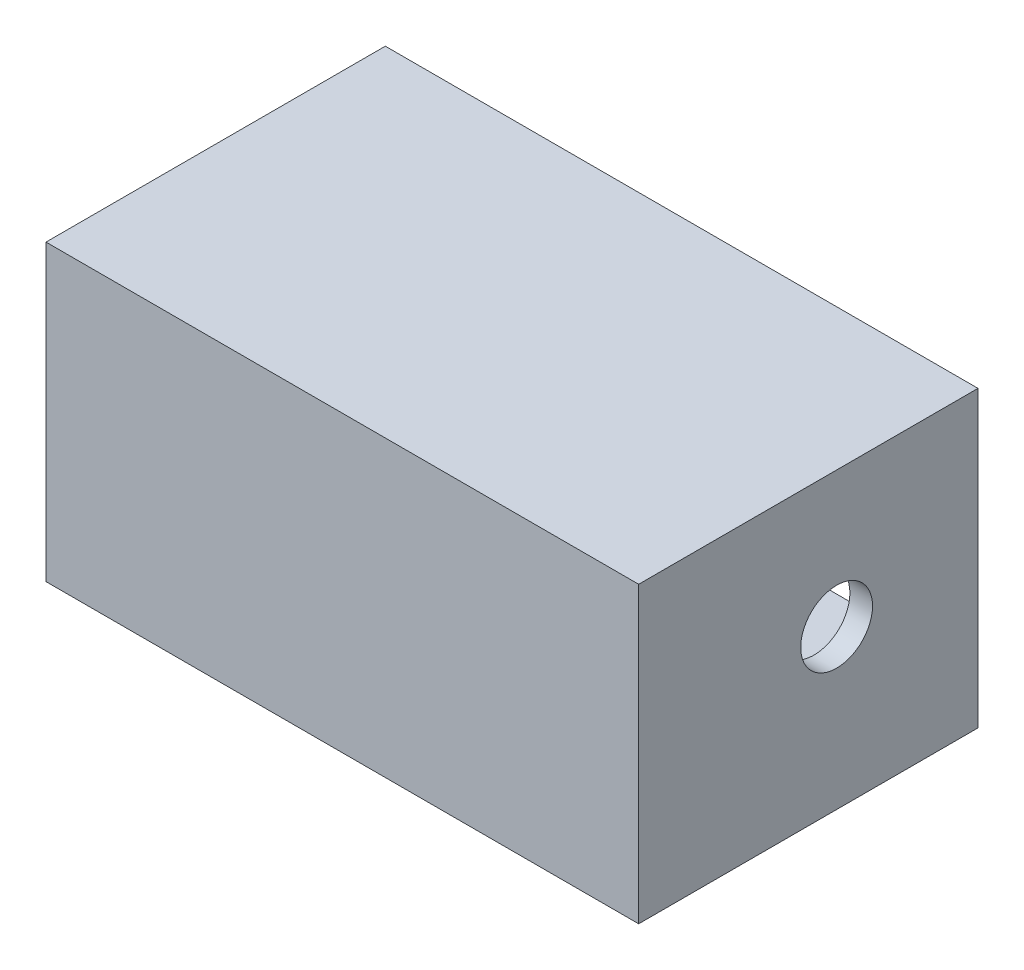
SolidWorks part; units mm, degrees
ref_plane "Front Plane" through (0, 0, 0) normal (0, 0, 1) x (1, 0, 0)
ref_plane "Top Plane" through (0, 0, 0) normal (0, 1, 0) x (1, 0, 0)
ref_plane "Right Plane" through (0, 0, 0) normal (1, 0, 0) x (0, 0, -1)
sketch "Sketch1" plane through (0, 0, 0) normal (0, 1, 0) x (1, 0, 0)
  line L1 (0, 0) -> (262, 0)
  line L2 (0, 0) -> (0, 150)
  line L3 (0, 150) -> (262, 150)
  line L4 (262, 0) -> (262, 150)
extrude "Boss-Extrude1" add sketch "Sketch1" along normal blind 20
sketch "Sketch2" plane through (0, 20, 0) normal (0, 1, 0) x (1, 0, 0)
  line L1 (0, 0) -> (262, 0)
  line L3 (10, 10) -> (252, 10)
  line L5 (262, 150) -> (0, 150) construction
  line L7 (0, 0) -> (0, 150)
  line L8 (0, 150) -> (10, 150)
  line L9 (10, 10) -> (10, 150)
  line L11 (262, 150) -> (252, 150)
  line L12 (262, 150) -> (262, 0)
  line L14 (252, 150) -> (252, 10)
  point P1 (0, 0)
extrude "Boss-Extrude2" add sketch "Sketch2" along normal blind 100
sketch "Sketch3" plane through (10, 0, 0) normal (1, 0, 0) x (0, 0, -1)
  circle A0 centre (87.5, 70) radius 14.2875
sketch "Sketch4" plane through (252, 0, 0) normal (1, 0, 0) x (0, 0, -1)
  circle A0 centre (87.5, 70) radius 15.875
extrude "Cut-Extrude1" cut sketch "Sketch3" against normal through all
extrude "Cut-Extrude2" cut sketch "Sketch4" along normal through all
sketch "Sketch5" plane through (0, 120, 0) normal (0, 1, 0) x (1, 0, 0)
  line L1 (0, 0) -> (262, 0)
  line L2 (0, 0) -> (0, 150)
  line L3 (0, 150) -> (262, 150)
  line L4 (262, 0) -> (262, 150)
extrude "Boss-Extrude4" add sketch "Sketch5" along normal blind 10
